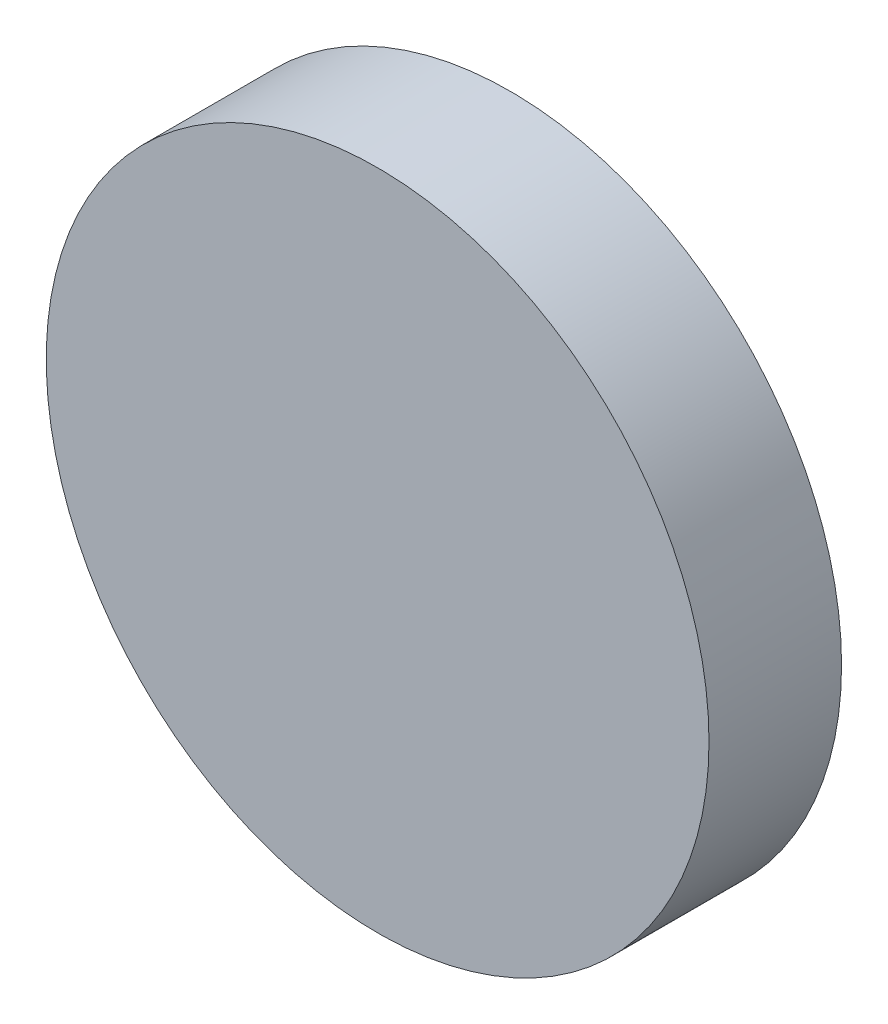
SolidWorks part; units mm, degrees
ref_plane "前视基准面" through (0, 0, 0) normal (0, 0, 1) x (1, 0, 0)
ref_plane "上视基准面" through (0, 0, 0) normal (0, 1, 0) x (1, 0, 0)
ref_plane "右视基准面" through (0, 0, 0) normal (1, 0, 0) x (0, 0, -1)
sketch "草图1" plane through (0, 0, 0) normal (0, 0, 1) x (1, 0, 0)
  circle A0 centre (0, 0) radius 5
  dimension "D1" = 10
extrude "凸台-拉伸1" add sketch "草图1" along normal blind 2
